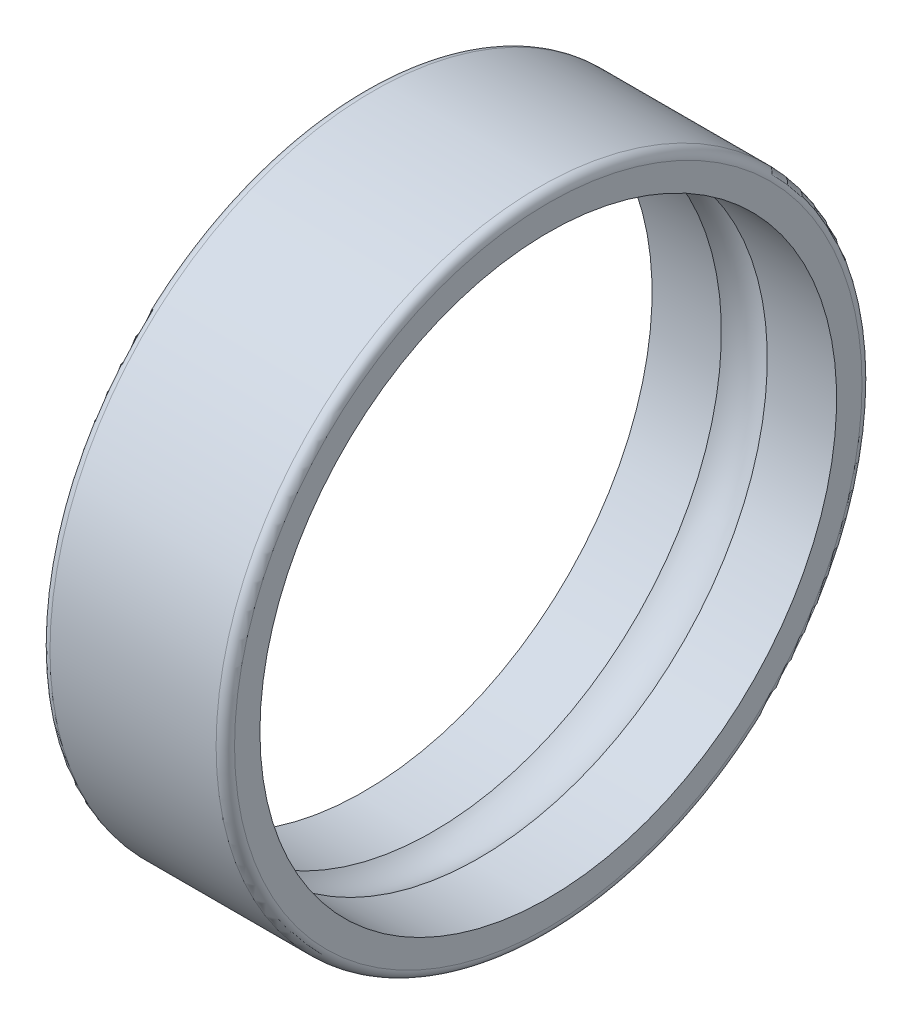
SolidWorks part; units mm, degrees
ref_plane "Front Plane" through (0, 0, 0) normal (0, 0, 1) x (1, 0, 0)
ref_plane "Top Plane" through (0, 0, 0) normal (0, 1, 0) x (1, 0, 0)
ref_plane "Right Plane" through (0, 0, 0) normal (1, 0, 0) x (0, 0, -1)
ref_plane "Plane1" through (0, 0, 0) normal (0, 0, 1) x (1, 0, 0)
sketch "Sketch1" plane through (0, 0, 0) normal (0, 0, 1) x (1, 0, 0)
  line L0 (0, 3.4) -> (0, 3.125)
  line L1 (0, 3.125) -> (0.7513, 3.125)
  line L2 (1.2487, 3.125) -> (2, 3.125)
  line L3 (2, 3.125) -> (2, 3.4)
  line L4 (1.9, 3.5) -> (0.1, 3.5)
  line L5 (2, 0) -> (0, 0) construction
  arc A0 (0.7513, 3.125) -> (1.2487, 3.125) centre (1, 2.75) cw
  arc A1 (2, 3.4) -> (1.9, 3.5) centre (1.9, 3.4) ccw
  arc A2 (0.1, 3.5) -> (0, 3.4) centre (0.1, 3.4) ccw
revolve "Revolve1" add sketch "Sketch1" angle 360 about L5
